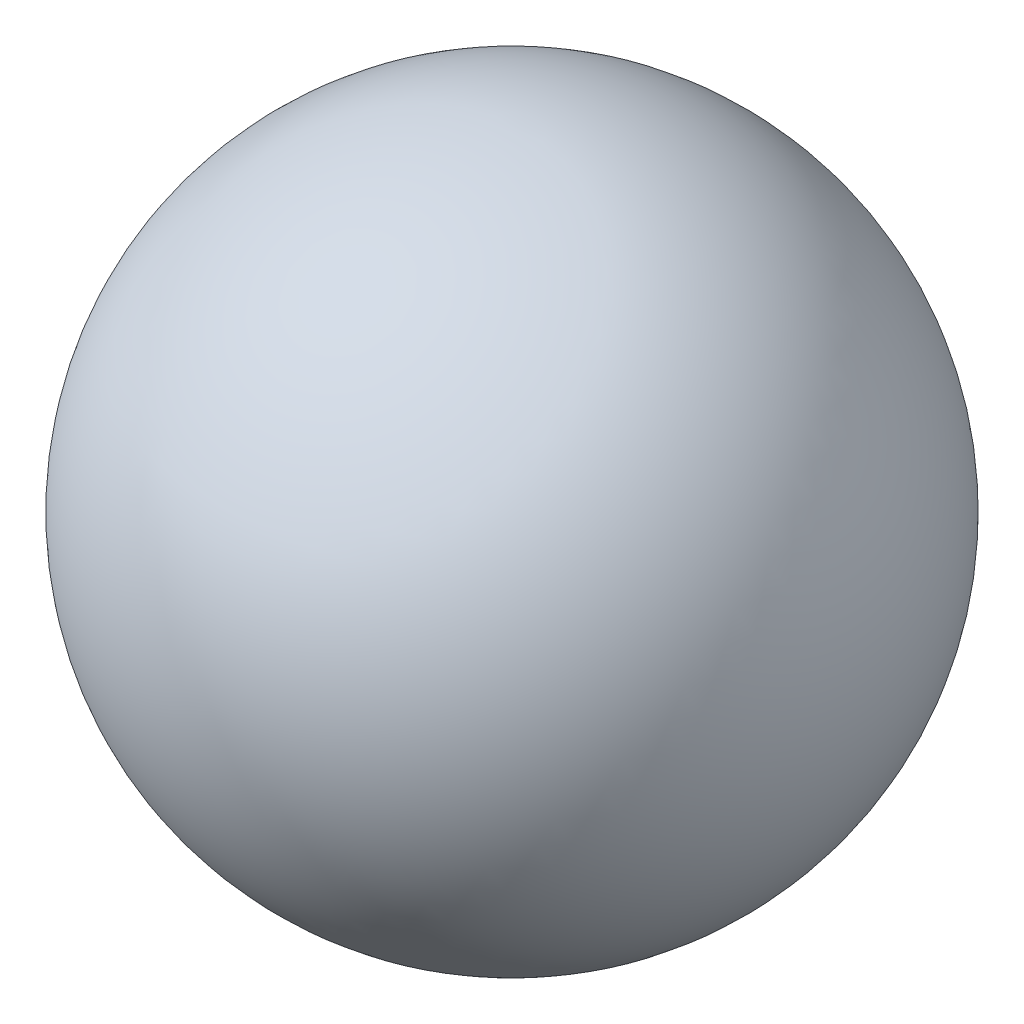
SolidWorks part; units mm, degrees
ref_plane "Front Plane" through (0, 0, 0) normal (0, 0, 1) x (1, 0, 0)
ref_plane "Top Plane" through (0, 0, 0) normal (0, 1, 0) x (1, 0, 0)
ref_plane "Right Plane" through (0, 0, 0) normal (1, 0, 0) x (0, 0, -1)
sketch "Sketch1" plane through (0, 0, 0) normal (0, 0, 1) x (1, 0, 0)
  line L0 (0, 0) -> (0, 152.4) construction
  line L1 (0, 0) -> (0, 152.4)
  arc A0 (0, 152.4) -> (0, 0) centre (0, 76.2) ccw
  dimension "D1" = 152.4
revolve "Revolve1" add sketch "Sketch1" angle 360 about L0
